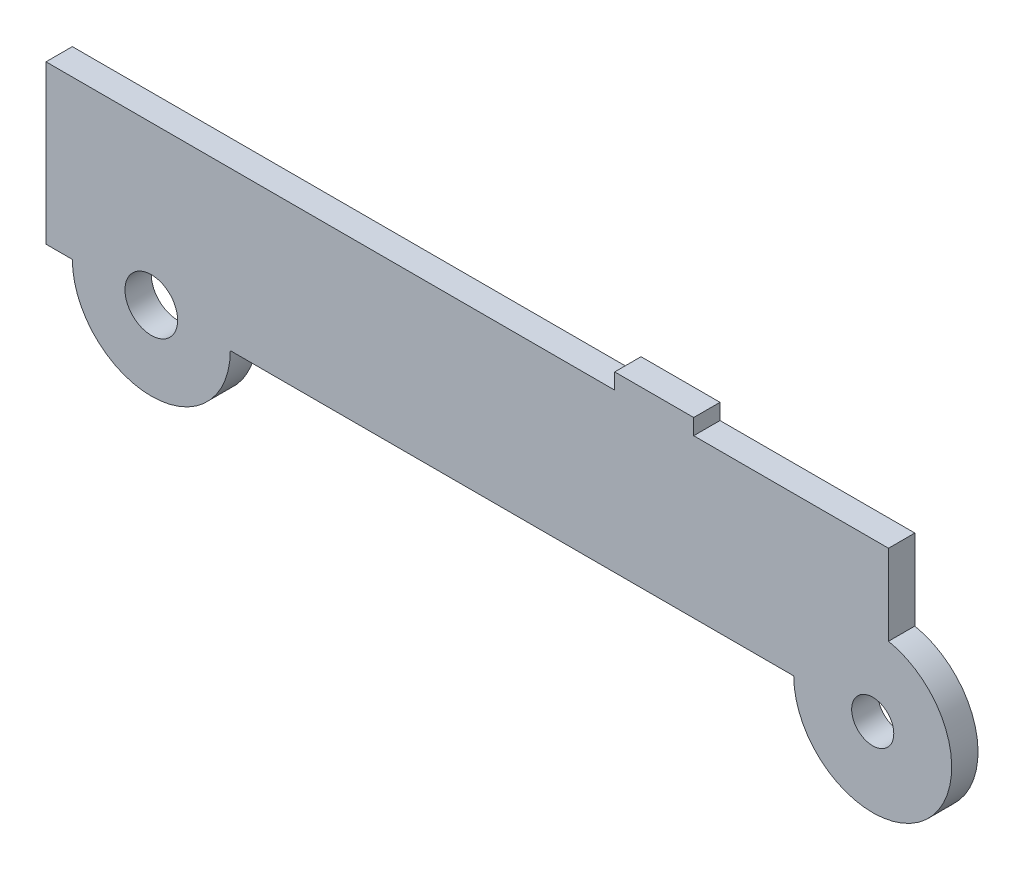
SolidWorks part; units mm, degrees
ref_plane "前视基准面" through (0, 0, 0) normal (0, 0, 1) x (1, 0, 0)
ref_plane "上视基准面" through (0, 0, 0) normal (0, 1, 0) x (1, 0, 0)
ref_plane "右视基准面" through (0, 0, 0) normal (1, 0, 0) x (0, 0, -1)
sketch "草图1" plane through (0, 0, 0) normal (0, 0, 1) x (1, 0, 0)
  line L1 (-80, -15) -> (80, -15)
  line L2 (-80, -15) -> (-80, 15)
  line L3 (-80, 15) -> (80, 15)
  line L4 (80, -15) -> (80, 15)
  line L5 (-80, -15) -> (80, 15) construction
  line L6 (-80, 15) -> (80, -15) construction
  point P0 (0, 0)
  dimension "D1" = 160
  dimension "D2" = 30
extrude "凸台-拉伸1" add sketch "草图1" along normal blind 5
sketch "草图2" plane through (0, 0, 5) normal (0, 0, 1) x (1, 0, 0)
  line L0 (-80, -15) -> (80, -15) construction
  line L1 (80, -15) -> (80, 15) construction
  line L2 (-80, 15) -> (-80, -15) construction
  circle A0 centre (-60, -15) radius 15
  circle A1 centre (77, -15) radius 15
  dimension "D1" = 30
  dimension "D4" = 30
  dimension "D2" = 3
  dimension "D3" = 20
extrude "凸台-拉伸2" add sketch "草图2" against normal blind 5
sketch "草图3" plane through (0, 0, 5) normal (0, 0, 1) x (1, 0, 0)
  circle A0 centre (-60, -15) radius 5
  circle A1 centre (77, -15) radius 4
  dimension "D1" = 8
  dimension "D2" = 10
extrude "切除-拉伸1" cut sketch "草图3" against normal through all
sketch "草图4" plane through (0, 15, 0) normal (0, 1, 0) x (1, 0, 0)
  line L0 (80, 0) -> (-80, 0) construction
  line L1 (28, 0) -> (43, 0)
  line L2 (28, 0) -> (28, -5)
  line L3 (28, -5) -> (43, -5)
  line L4 (43, 0) -> (43, -5)
  line L5 (80, -5) -> (-80, -5) construction
  line L6 (80, -5) -> (80, 0) construction
  point P8 (43, -2.5)
  dimension "D1" = 37
  dimension "D2" = 15
extrude "凸台-拉伸3" add sketch "草图4" along normal blind 3
